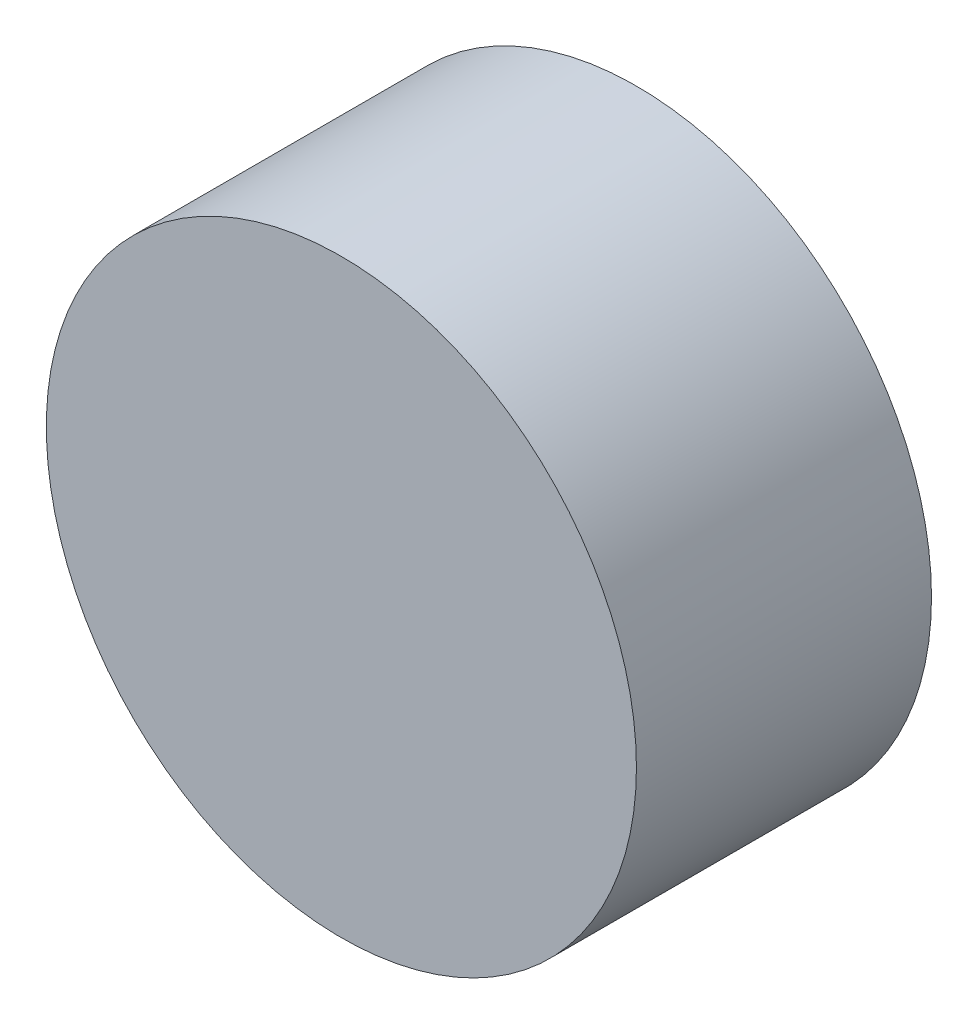
SolidWorks part; units mm, degrees
ref_plane "Front Plane" through (0, 0, 0) normal (0, 0, 1) x (1, 0, 0)
ref_plane "Top Plane" through (0, 0, 0) normal (0, 1, 0) x (1, 0, 0)
ref_plane "Right Plane" through (0, 0, 0) normal (1, 0, 0) x (0, 0, -1)
sketch "Sketch1" plane through (0, 0, 0) normal (0, 0, 1) x (1, 0, 0)
  circle A0 centre (0, 0) radius 100
  dimension "D1" = 200
extrude "Boss-Extrude1" add sketch "Sketch1" along normal blind 100
